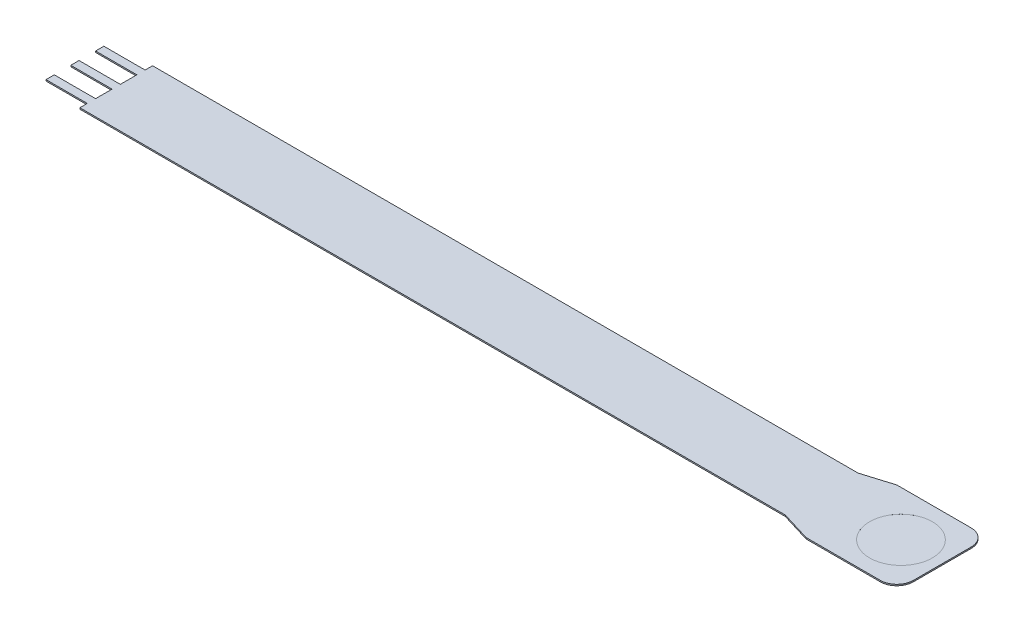
SolidWorks part; units mm, degrees
ref_plane "Front Plane" through (0, 0, 0) normal (0, 0, 1) x (1, 0, 0)
ref_plane "Top Plane" through (0, 0, 0) normal (0, 1, 0) x (1, 0, 0)
ref_plane "Right Plane" through (0, 0, 0) normal (1, 0, 0) x (0, 0, -1)
sketch "Sketch1" plane through (0, 0, 0) normal (0, 1, 0) x (1, 0, 0)
  line L0 (-118.11, -6.985) -> (-118.11, 6.985) construction
  line L1 (-76.2, -6.985) -> (-76.2, 6.985) construction
  line L2 (-120.65, -0.635) -> (-127, -0.635)
  line L3 (-7.62, 6.985) -> (6.35, 6.985)
  line L4 (-120.65, 5.588) -> (-120.65, 4.445)
  line L6 (6.35, 6.985) -> (6.35, -6.985)
  line L7 (-120.65, 0.635) -> (-120.65, 3.175) construction
  line L9 (-120.65, 0.635) -> (-127, 0.635)
  line L10 (-127, -0.635) -> (-127, 0.635)
  line L11 (-120.65, 3.175) -> (-127, 3.175)
  line L13 (-120.65, 4.445) -> (-127, 4.445)
  line L14 (-127, 3.175) -> (-127, 4.445)
  line L15 (-120.65, -3.175) -> (-127, -3.175)
  line L17 (-120.65, -4.445) -> (-127, -4.445)
  line L18 (-127, -3.175) -> (-127, -4.445)
  line L19 (-120.65, 3.175) -> (-120.65, 0.635)
  line L20 (-120.65, 4.445) -> (-120.65, 5.588) construction
  line L21 (-120.65, -0.635) -> (-120.65, -3.175)
  line L23 (-120.65, 5.588) -> (-108.7487, 5.588)
  line L24 (-113.0069, 0) -> (0, 0) construction
  line L25 (-108.7487, 0) -> (-108.7487, 5.588) construction
  line L26 (-108.7487, 0) -> (-108.7487, -5.588) construction
  line L27 (-108.7487, 5.588) -> (-12.192, 5.588)
  line L28 (-12.192, 5.588) -> (-7.62, 6.985)
  line L29 (-7.62, -6.985) -> (6.35, -6.985)
  line L30 (-12.192, -5.588) -> (-7.62, -6.985)
  line L31 (-108.7487, -5.588) -> (-12.192, -5.588)
  line L32 (-120.65, -5.588) -> (-108.7487, -5.588)
  line L33 (-120.65, -5.588) -> (-120.65, -4.445)
  circle A0 centre (0, 0) radius 4.826 construction
  point P3 (6.35, 0)
  point P4 (-7.62, 6.985)
  point P7 (-76.2, 0)
  point P24 (-127, 0)
  point P27 (-118.11, 0)
  dimension "D1" = 9.652
  dimension "D2" = 6.35
  dimension "D3" = 13.97
  dimension "D4" = 11.176
  dimension "D5" = 6.35
  dimension "D6" = 1.27
  dimension "D7" = 2.54
  dimension "D8" = 2.54
  dimension "D9" = 18.542
  dimension "D10" = 6.985
  dimension "D12" = 76.2
  dimension "D14" = 13.97
extrude "Boss-Extrude1" add sketch "Sketch1" along normal blind 0.2032
sketch "Sketch2" plane through (0, 0.2032, 0) normal (0, 1, 0) x (1, 0, 0)
  circle A0 centre (0, 0) radius 4.826
extrude "Cut-Extrude1" cut sketch "Sketch2" against normal blind 0.0025
fillet "Fillet1" radius 2.54 2 edges at (6.35, 0.1016, -6.985) (6.35, 0.1016, 6.985)
